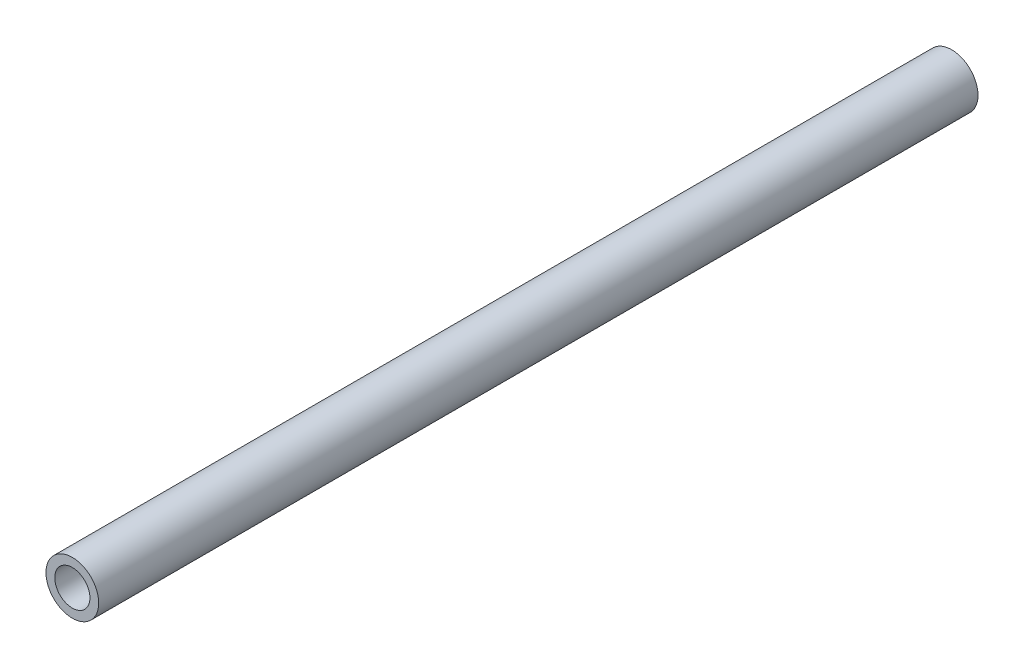
SolidWorks part; units mm, degrees
ref_plane "Front Plane" through (0, 0, 0) normal (0, 0, 1) x (1, 0, 0)
ref_plane "Top Plane" through (0, 0, 0) normal (0, 1, 0) x (1, 0, 0)
ref_plane "Right Plane" through (0, 0, 0) normal (1, 0, 0) x (0, 0, -1)
sketch "Sketch1" plane through (0, 0, 0) normal (0, 0, 1) x (1, 0, 0)
  circle A0 centre (0, 0) radius 2 construction
  circle A1 centre (0, 0) radius 3
  dimension "D1" = 4
  dimension "D2" = 6
extrude "Boss-Extrude1" add sketch "Sketch1" along normal mid plane 100
hole_wizard "Ø4.0mm Dowel Hole1" positions "Sketch3" profile "Sketch2" hole size "Ø4.0" standard "ISO" end condition up to next
sketch "Sketch3" plane through (0, 0, 50) normal (0, 0, 1) x (1, 0, 0)
  point P0 (0, 0)
sketch "Sketch2" plane through (0, 0, 50) normal (1, 0, 0) x (0, -1, 0)
  line L0 (0, 0) -> (0, 100)
  line L1 (0, 100) -> (2, 100)
  line L2 (2, 100) -> (2, 0)
  line L5 (2, 0) -> (0, 0)
  line L11 (0, -6.35) -> (0, 107.95) construction
  dimension "Thru Hole Dia." = 4
  dimension "Thru Hole Depth" = 100
